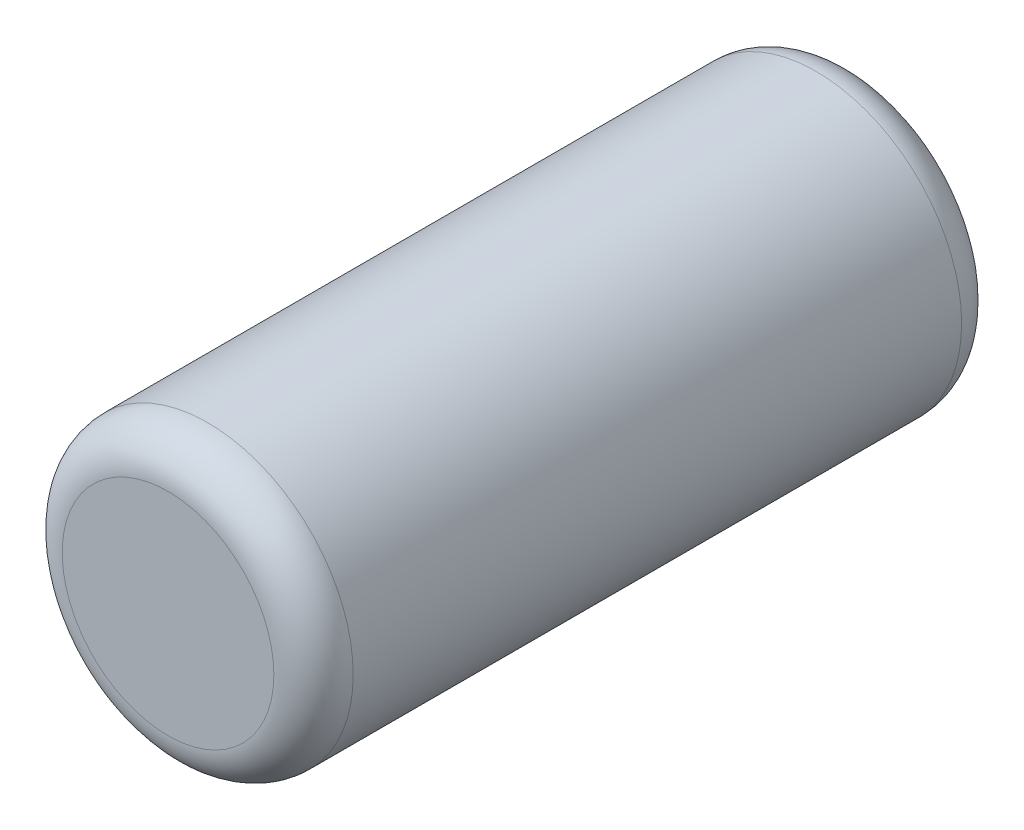
SolidWorks part; units mm, degrees
ref_plane "Front Plane" through (0, 0, 0) normal (0, 0, 1) x (1, 0, 0)
ref_plane "Top Plane" through (0, 0, 0) normal (0, 1, 0) x (1, 0, 0)
ref_plane "Right Plane" through (0, 0, 0) normal (1, 0, 0) x (0, 0, -1)
sketch "Sketch2" plane through (0, 0, 0) normal (0, 0, 1) x (1, 0, 0)
  circle A0 centre (0, 0) radius 5.5
  dimension "D1" = 11
extrude "Boss-Extrude1" add sketch "Sketch2" along normal mid plane 26
fillet "Fillet1" radius 1.5 2 edges at (5.5, 0, -13) (5.5, 0, 13)
